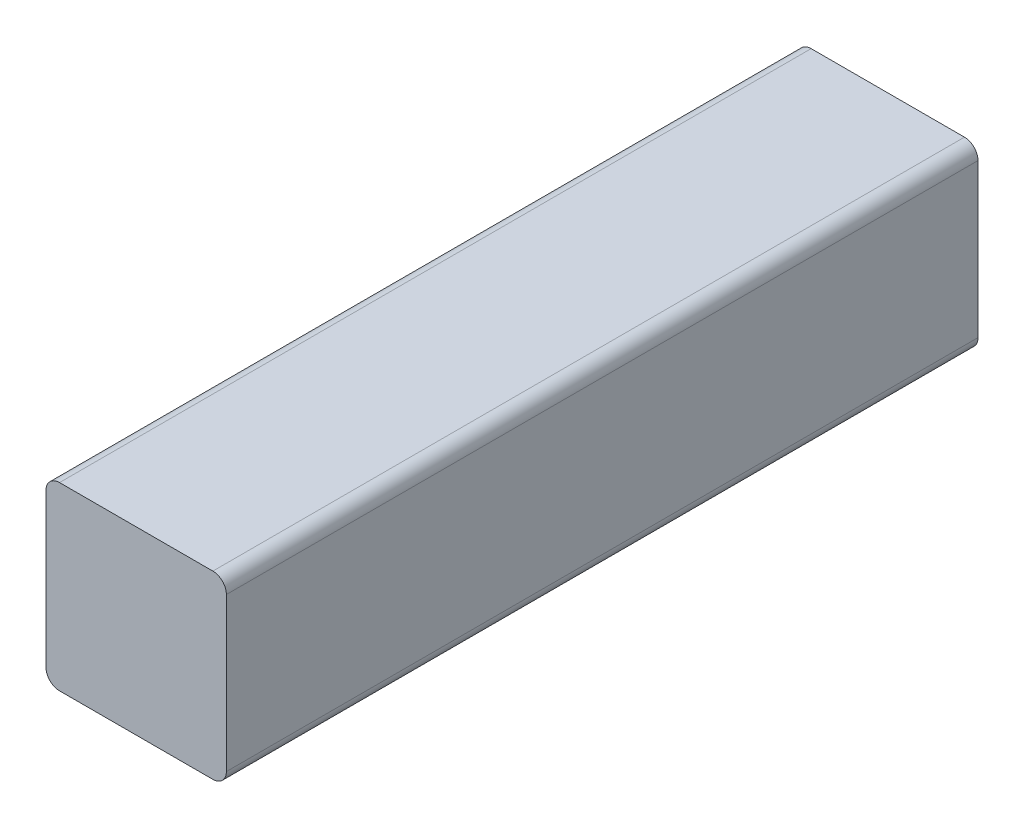
SolidWorks part; units mm, degrees
ref_plane "Plan de face" through (0, 0, 0) normal (0, 0, 1) x (1, 0, 0)
ref_plane "Plan de dessus" through (0, 0, 0) normal (0, 1, 0) x (1, 0, 0)
ref_plane "Plan de droite" through (0, 0, 0) normal (1, 0, 0) x (0, 0, -1)
sketch "Esquisse1" plane through (0, 0, 0) normal (0, 0, 1) x (1, 0, 0)
  line L0 (0, -63.3691) -> (0, 71.2902) construction
  line L1 (-75.6108, 0) -> (80.6515, 0) construction
  line L2 (-15, 12.75) -> (-15, -12.75)
  line L3 (-12.75, 15) -> (12.75, 15)
  line L4 (-12.75, -15) -> (12.75, -15)
  line L6 (15, 12.75) -> (15, -12.75)
  arc A0 (12.75, 15) -> (15, 12.75) centre (12.75, 12.75) cw
  arc A1 (-12.75, 15) -> (-15, 12.75) centre (-12.75, 12.75) ccw
  arc A2 (-12.75, -15) -> (-15, -12.75) centre (-12.75, -12.75) cw
  arc A3 (12.75, -15) -> (15, -12.75) centre (12.75, -12.75) ccw
  point P5 (-15, 0)
  point P14 (0, 15)
  point P20 (0, -15)
  point P21 (15, 0)
  dimension "D3" = 2.25
  dimension "D1" = 30
  dimension "D2" = 30
extrude "Extrusion1" add sketch "Esquisse1" along normal blind 125
